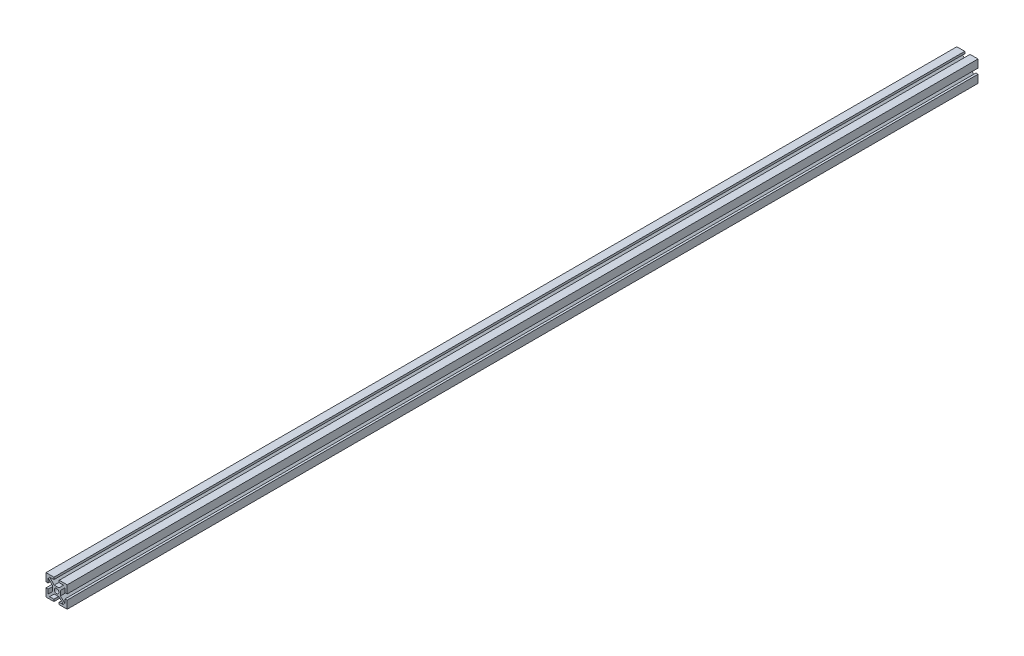
SolidWorks part; units mm, degrees
material "6061-T6 (SS)"
ref_plane "Plan de face" through (0, 0, 0) normal (0, 0, 1) x (1, 0, 0)
ref_plane "Plan de dessus" through (0, 0, 0) normal (0, 1, 0) x (1, 0, 0)
ref_plane "Plan de droite" through (0, 0, 0) normal (1, 0, 0) x (0, 0, -1)
sketch "Esquisse1" plane through (0, 0, 0) normal (0, 0, 1) x (1, 0, 0)
  line L0 (0, 0) -> (0, 68.6636) construction
  line L1 (-10, 10) -> (10, 10)
  line L2 (-10, 10) -> (-10, -10)
  line L3 (-10, -10) -> (10, -10)
  line L4 (10, 10) -> (10, -10)
  line L5 (-3.65, 3.65) -> (3.65, 3.65)
  line L6 (-3.65, 3.65) -> (-3.65, -3.65)
  line L7 (-3.65, -3.65) -> (3.65, -3.65)
  line L8 (3.65, 3.65) -> (3.65, -3.65)
  line L9 (0, 68.6636) -> (0, 0) construction
  line L10 (0, 0) -> (78.2836, 0) construction
  line L11 (-10, 10) -> (10, -10) construction
  line L12 (-2.5, 10) -> (2.5, 10)
  line L13 (-2.5, 10) -> (-2.5, 8)
  line L14 (-2.5, 8) -> (2.5, 8)
  line L15 (2.5, 10) -> (2.5, 8)
  line L16 (10, 2.5) -> (8, 2.5)
  line L17 (10, 2.5) -> (10, -2.5)
  line L18 (10, -2.5) -> (8, -2.5)
  line L19 (8, 2.5) -> (8, -2.5)
  line L20 (2.5, -10) -> (-2.5, -10)
  line L21 (2.5, -10) -> (2.5, -8)
  line L22 (2.5, -8) -> (-2.5, -8)
  line L23 (-2.5, -10) -> (-2.5, -8)
  line L24 (-10, -2.5) -> (-8, -2.5)
  line L25 (-10, -2.5) -> (-10, 2.5)
  line L26 (-10, 2.5) -> (-8, 2.5)
  line L27 (-8, -2.5) -> (-8, 2.5)
  line L28 (10, 10) -> (-10, -10) construction
  line L29 (-8, 2.5) -> (-8, 6.5858)
  line L30 (-8, 6.5858) -> (-3.65, 2.2358)
  line L31 (-3.65, 2.2358) -> (-3.65, -2.2358)
  line L32 (-3.65, -2.2358) -> (-8, -6.5858)
  line L33 (-8, -6.5858) -> (-8, -2.5)
  line L34 (-2.5, -8) -> (-6.5858, -8)
  line L35 (-6.5858, -8) -> (-2.2358, -3.65)
  line L36 (-2.2358, -3.65) -> (2.2358, -3.65)
  line L37 (2.2358, -3.65) -> (6.5858, -8)
  line L38 (6.5858, -8) -> (2.5, -8)
  line L39 (8, -6.5858) -> (3.65, -2.2358)
  line L40 (3.65, -2.2358) -> (3.65, 2.2358)
  line L41 (3.65, 2.2358) -> (8, 6.5858)
  line L42 (8, 6.5858) -> (8, 2.5)
  line L43 (8, 2.5) -> (8.0085, 2.747)
  line L44 (8, -2.5) -> (8, -6.5858)
  line L45 (2.5, 8) -> (6.5858, 8)
  line L46 (6.5858, 8) -> (2.2358, 3.65)
  line L47 (2.2358, 3.65) -> (-2.2358, 3.65)
  line L48 (-2.2358, 3.65) -> (-6.5858, 8)
  line L49 (-6.5858, 8) -> (-2.5, 8)
  circle A0 centre (0, 0) radius 2.15
  dimension "D1" = 4.3
  dimension "D2" = 6.35
  dimension "D3" = 6.35
  dimension "D4" = 6.35
  dimension "D5" = 6.35
  dimension "D6" = 20
  dimension "D7" = 20
  dimension "D8" = 5
  dimension "D9" = 5
  dimension "D10" = 5
  dimension "D11" = 5
  dimension "D12" = 2
  dimension "D13" = 2
  dimension "D14" = 2
  dimension "D15" = 2
  dimension "D16" = 2
  dimension "D17" = 2
  dimension "D18" = 2
  dimension "D19" = 2
extrude "Boss.-Extru.1" add sketch "Esquisse1" along normal blind 860
